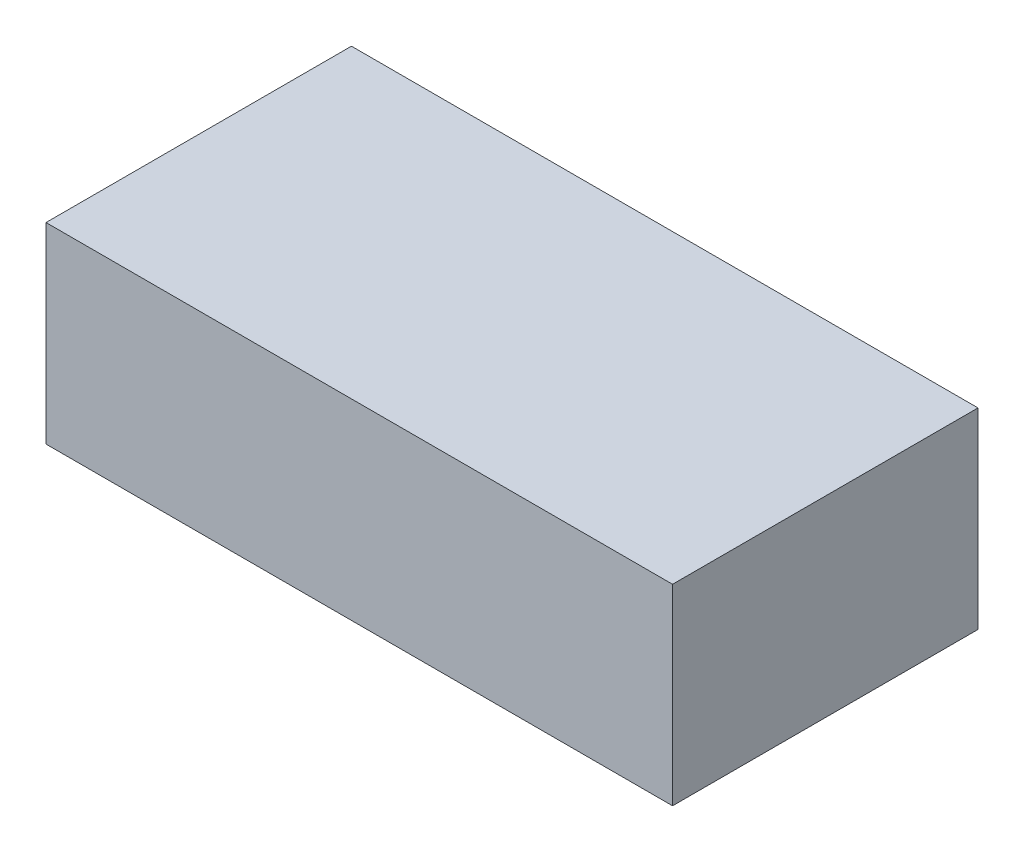
SolidWorks part; units mm, degrees
ref_plane "Front Plane" through (0, 0, 0) normal (0, 0, 1) x (1, 0, 0)
ref_plane "Top Plane" through (0, 0, 0) normal (0, 1, 0) x (1, 0, 0)
ref_plane "Right Plane" through (0, 0, 0) normal (1, 0, 0) x (0, 0, -1)
sketch "Sketch1" plane through (0, 0, 0) normal (0, 1, 0) x (1, 0, 0)
  line L1 (-40, -19.5) -> (40, -19.5)
  line L2 (-40, -19.5) -> (-40, 19.5)
  line L3 (-40, 19.5) -> (40, 19.5)
  line L4 (40, -19.5) -> (40, 19.5)
  line L5 (-40, -19.5) -> (40, 19.5) construction
  line L6 (-40, 19.5) -> (40, -19.5) construction
  point P0 (0, 0)
  dimension "D1" = 80
  dimension "D2" = 39
extrude "Boss-Extrude1" add sketch "Sketch1" along normal blind 24.5
